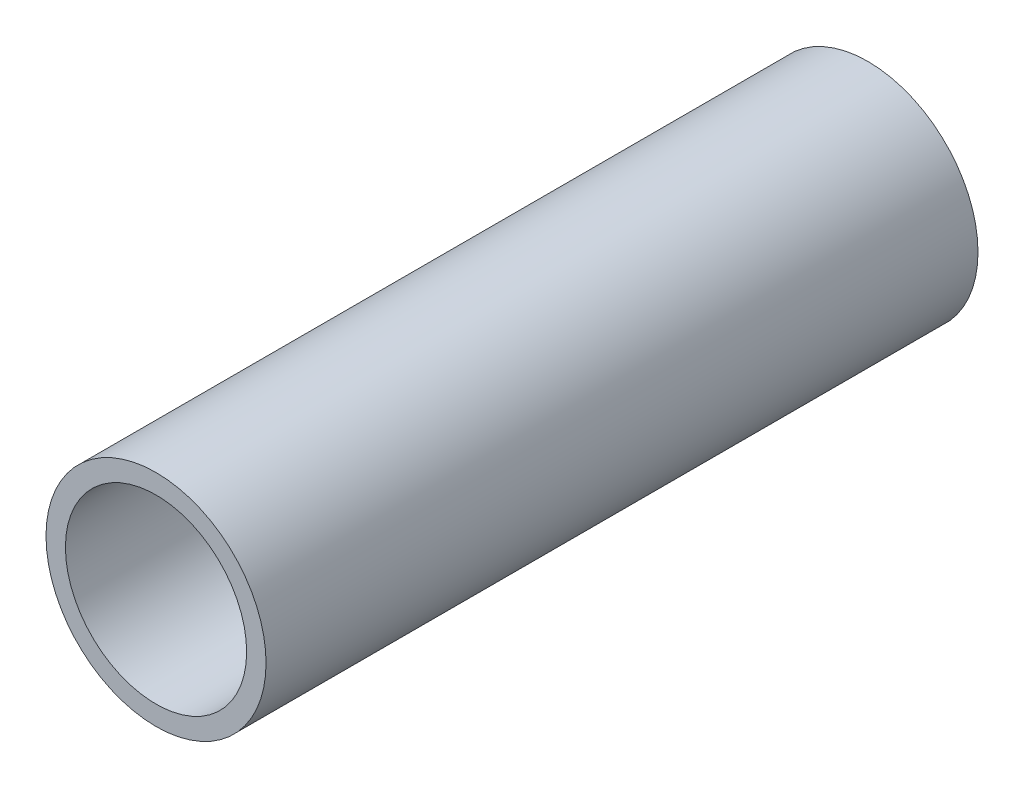
SolidWorks part; units mm, degrees
material "Plain Carbon Steel"
ref_plane "Front Plane" through (0, 0, 0) normal (0, 0, 1) x (1, 0, 0)
ref_plane "Top Plane" through (0, 0, 0) normal (0, 1, 0) x (1, 0, 0)
ref_plane "Right Plane" through (0, 0, 0) normal (1, 0, 0) x (0, 0, -1)
sketch "Sketch1" plane through (0, 0, 0) normal (0, 0, 1) x (1, 0, 0)
  circle A0 centre (347.5, -26) radius 14
  circle A1 centre (347.5, -26) radius 17
  dimension "D1" = 28
  dimension "D2" = 34
extrude "Boss-Extrude1" add sketch "Sketch1" against normal offset from surface (110 mm away) 30
